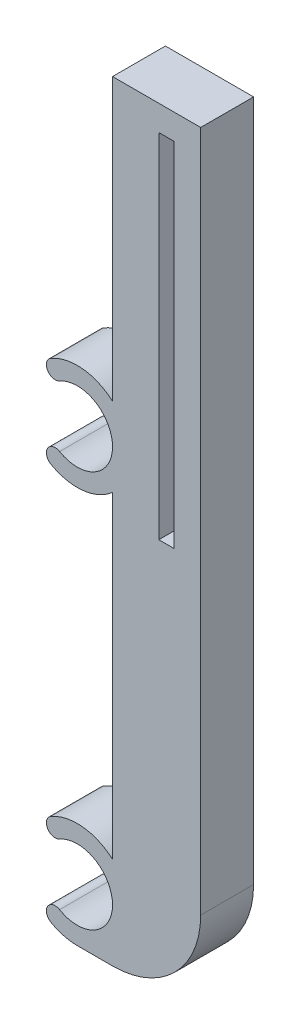
SolidWorks part; units mm, degrees
ref_plane "Front Plane" through (0, 0, 0) normal (0, 0, 1) x (1, 0, 0)
ref_plane "Top Plane" through (0, 0, 0) normal (0, 1, 0) x (1, 0, 0)
ref_plane "Right Plane" through (0, 0, 0) normal (1, 0, 0) x (0, 0, -1)
sketch "Sketch1" plane through (0, 0, 0) normal (0, 0, 1) x (1, 0, 0)
  line L5 (17.5, 87.375) -> (17.5, 10)
  line L7 (3.5, 6) -> (3.5, -1.2431) construction
  line L8 (7.5, 10.4721) -> (7.5, -1.6862) construction
  line L9 (3.5, 0) -> (7.5, 0)
  line L10 (7.5, 87.375) -> (7.5, 55.4721)
  line L11 (7.5, 87.375) -> (17.5, 87.375)
  line L12 (7.5, 10.4721) -> (7.5, 46.5279)
  arc A11 (7.5, 0) -> (17.5, 10) centre (7.5, 10) ccw
  arc A12 (3.5, 0) -> (0.5, 0.8038) centre (3.5, 6) cw
  arc A13 (0.5, 0.8038) -> (1.5, 2.5359) centre (1, 1.6699) cw
  arc A14 (0.5, 11.1962) -> (7.5, 10.4721) centre (3.5, 6) cw
  arc A15 (1.5, 9.4641) -> (1.5, 2.5359) centre (3.5, 6) cw
  arc A16 (1.5, 9.4641) -> (0.5, 11.1962) centre (1, 10.3301) cw
  arc A17 (7.5, 46.5279) -> (0.5, 45.8038) centre (3.5, 51) cw
  arc A18 (0.5, 45.8038) -> (1.5, 47.5359) centre (1, 46.6699) cw
  arc A19 (0.5, 56.1962) -> (7.5, 55.4721) centre (3.5, 51) cw
  arc A20 (1.5, 54.4641) -> (1.5, 47.5359) centre (3.5, 51) cw
  arc A21 (1.5, 54.4641) -> (0.5, 56.1962) centre (1, 55.3301) cw
  dimension "D1" = 77.375
  dimension "D2" = 36.0557
extrude "Boss-Extrude-Base" add sketch "Sketch1" along normal blind 6
sketch "Sketch4" plane through (0, 0, 6) normal (0, 0, 1) x (1, 0, 0)
  line L7 (12.75, 84.5) -> (12.75, 44.5)
  line L8 (14.5, 44.5) -> (12.75, 44.5)
  line L9 (14.5, 84.5) -> (14.5, 44.5)
  line L10 (14.5, 84.5) -> (12.75, 84.5)
  dimension "D1" = 3
  dimension "D2" = 2.875
  dimension "D3" = 40
extrude "Cut-Extrude-Slot" cut sketch "Sketch4" against normal blind 4.5
